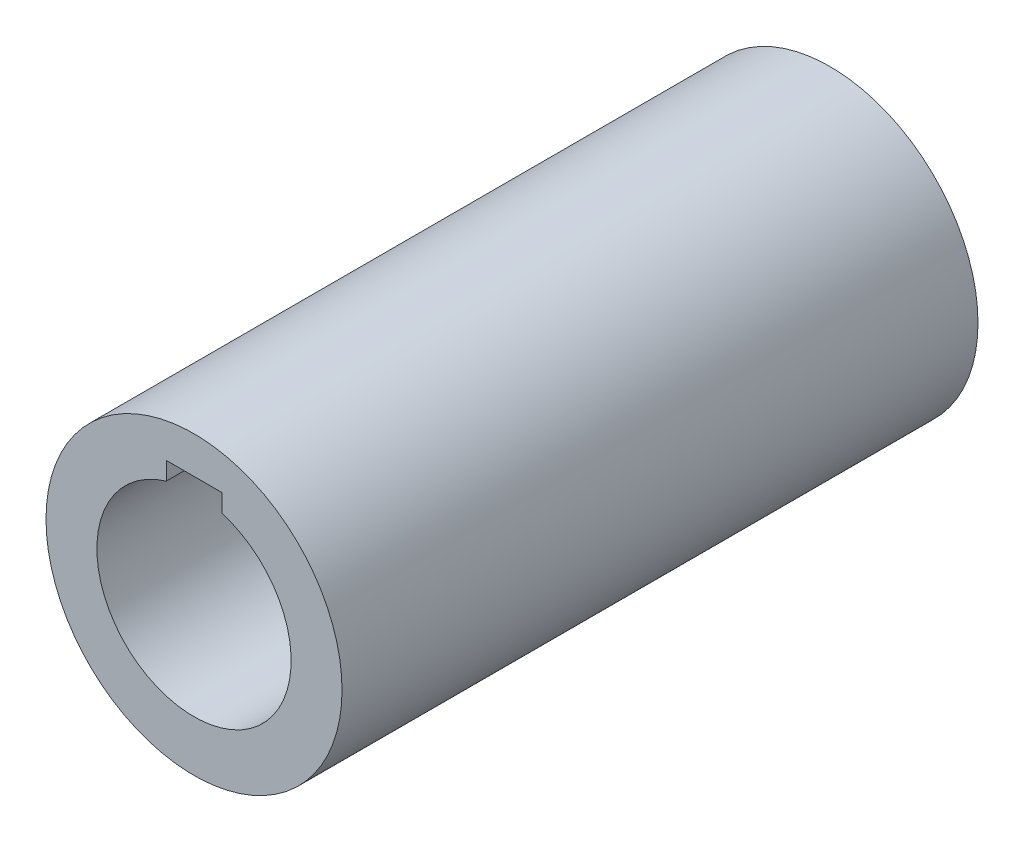
SolidWorks part; units mm, degrees
ref_plane "Front Plane" through (0, 0, 0) normal (0, 0, 1) x (1, 0, 0)
ref_plane "Top Plane" through (0, 0, 0) normal (0, 1, 0) x (1, 0, 0)
ref_plane "Right Plane" through (0, 0, 0) normal (1, 0, 0) x (0, 0, -1)
sketch "Sketch1" plane through (0, 0, 0) normal (0, 0, 1) x (1, 0, 0)
  circle A0 centre (0, 0) radius 21
  circle A1 centre (0, 0) radius 32
  dimension "D1" = 64
  dimension "D2" = 42
extrude "Boss-Extrude1" add sketch "Sketch1" along normal blind 137.5
sketch "Sketch2" plane through (0, 0, 137.5) normal (0, 0, 1) x (1, 0, 0)
  line L1 (-6, 24) -> (6, 24)
  line L2 (-6, 24) -> (-6, 20.1246)
  line L3 (-6, 20.1246) -> (6, 20.1246)
  line L4 (6, 24) -> (6, 20.1246)
  circle A0 centre (0, 0) radius 21 construction
  point P6 (0, 0)
  dimension "D1" = 12
  dimension "D2" = 24
extrude "Cut-Extrude1" cut sketch "Sketch2" against normal through all
